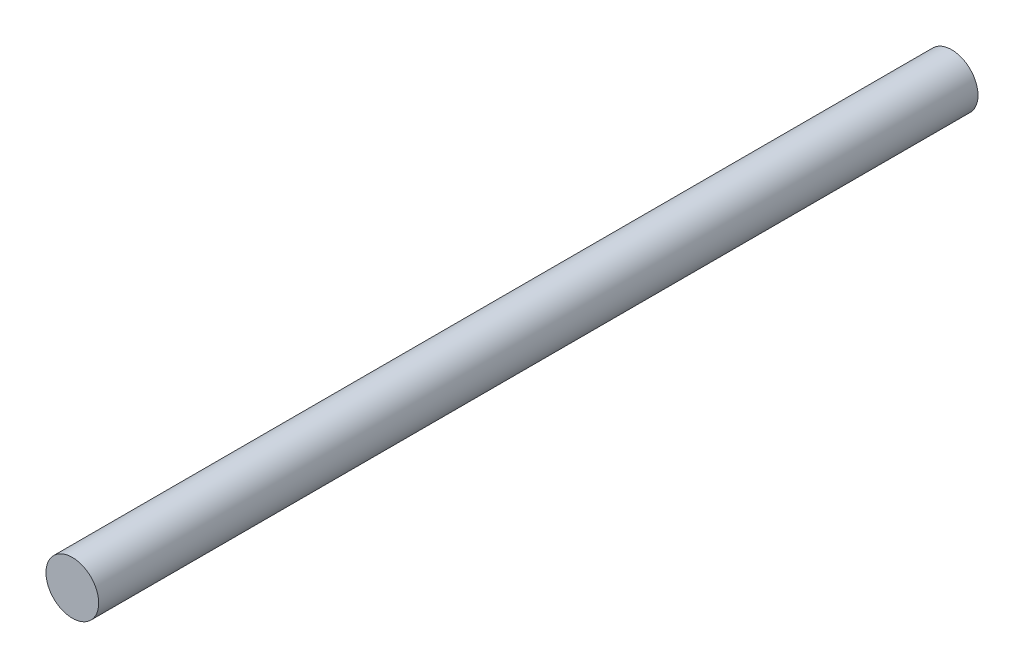
SolidWorks part; units mm, degrees
ref_plane "Piano frontale" through (0, 0, 0) normal (0, 0, 1) x (1, 0, 0)
ref_plane "Piano superiore" through (0, 0, 0) normal (0, 1, 0) x (1, 0, 0)
ref_plane "Piano destro" through (0, 0, 0) normal (1, 0, 0) x (0, 0, -1)
sketch "Schizzo1" plane through (0, 0, 0) normal (0, 0, 1) x (1, 0, 0)
  circle A0 centre (115, -2) radius 3
  dimension "D1" = 6
  dimension "D2" = 2
  dimension "D3" = 115
extrude "Estrusione-Estrusione1" add sketch "Schizzo1" against normal blind 100
